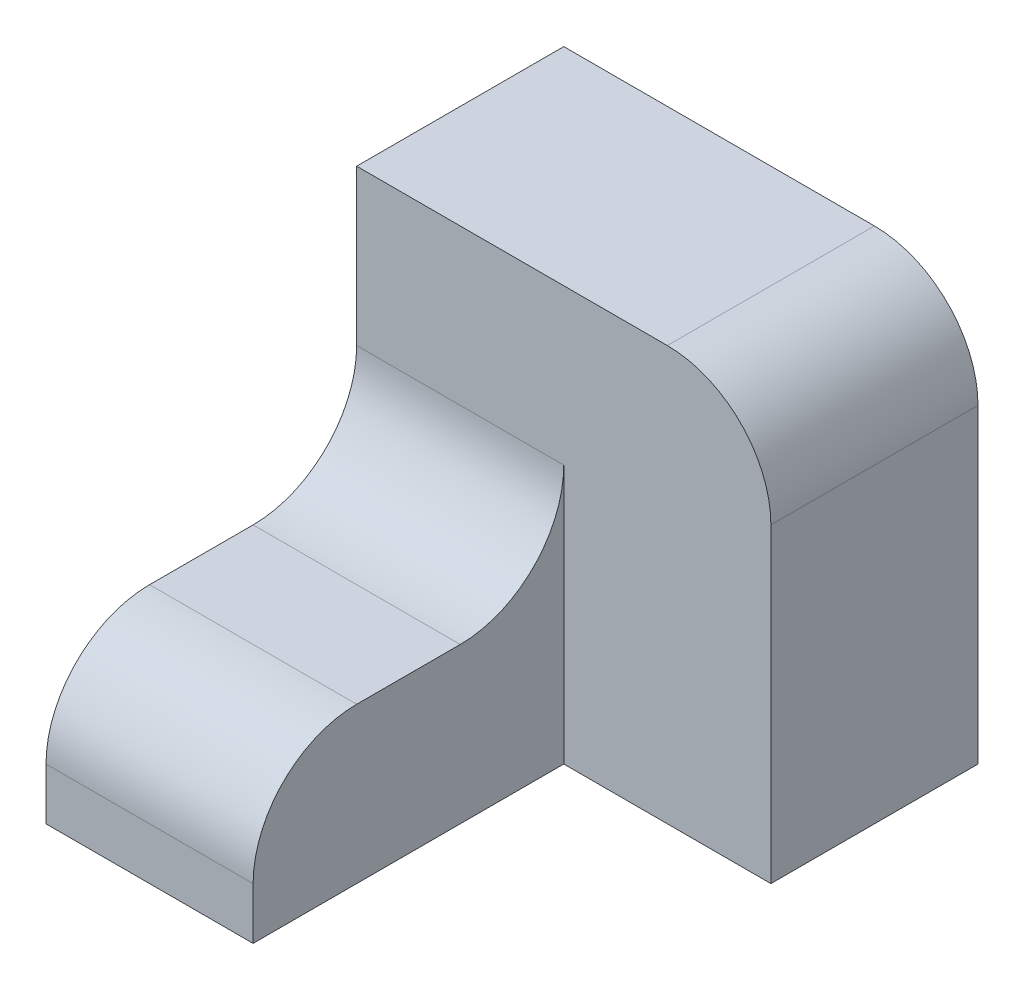
SolidWorks part; units mm, degrees
ref_plane "Front Plane" through (0, 0, 0) normal (0, 0, 1) x (1, 0, 0)
ref_plane "Top Plane" through (0, 0, 0) normal (0, 1, 0) x (1, 0, 0)
ref_plane "Right Plane" through (0, 0, 0) normal (1, 0, 0) x (0, 0, -1)
sketch "Sketch1" plane through (0, 0, 0) normal (0, 0, 1) x (1, 0, 0)
  line L1 (-30, -15) -> (-10, -15)
  line L2 (-10, -15) -> (-10, 0)
  line L3 (-10, 0) -> (-30, 0)
  line L4 (-30, 0) -> (-30, -15)
  dimension "D1" = 20
  dimension "Width" = 15
extrude "Boss-Extrude1" add sketch "Sketch1" along normal blind 30
sketch "Sketch2" plane through (0, 0, 0) normal (0, 0, 1) x (1, 0, 0)
  line L1 (-30, -15) -> (10, -15)
  line L2 (10, -15) -> (10, 25)
  line L3 (10, 25) -> (-30, 25)
  line L4 (-30, 25) -> (-30, -15)
  dimension "D1" = 40
  dimension "Width" = 40
extrude "Boss-Extrude2" add sketch "Sketch2" against normal blind 20
fillet "Fillet1" radius 10 3 edges at (-20, 0, 0) (10, 25, -10) (-20, 0, 30)
